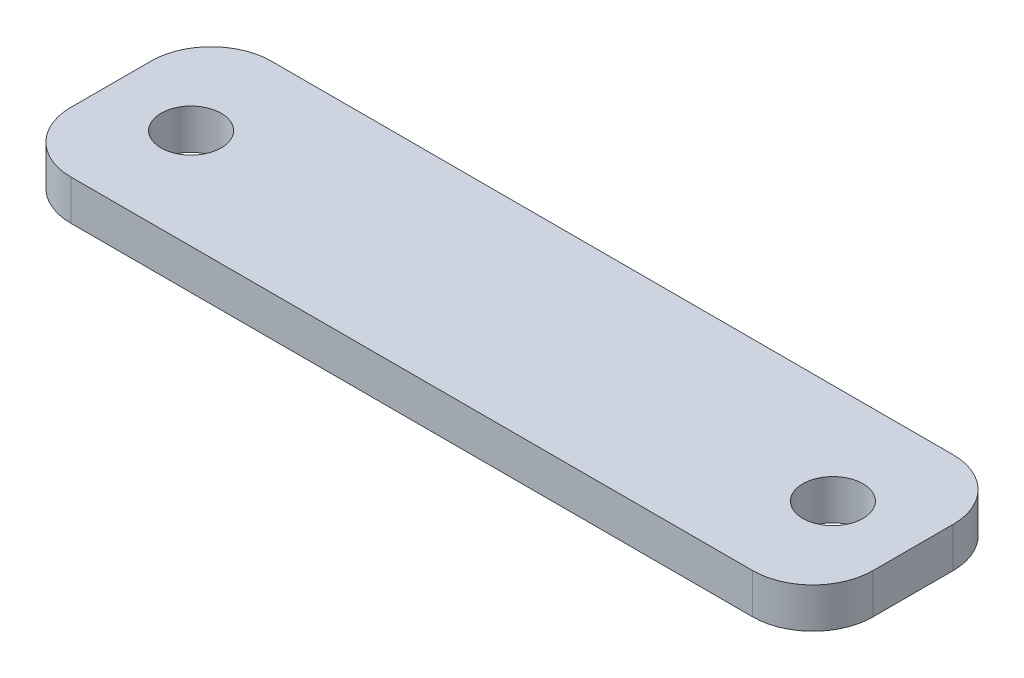
SolidWorks part; units mm, degrees
ref_plane "Front Plane" through (0, 0, 0) normal (0, 0, 1) x (1, 0, 0)
ref_plane "Top Plane" through (0, 0, 0) normal (0, 1, 0) x (1, 0, 0)
ref_plane "Right Plane" through (0, 0, 0) normal (1, 0, 0) x (0, 0, -1)
sketch "Sketch1" plane through (0, 0, 0) normal (0, 1, 0) x (1, 0, 0)
  line L1 (-20, 5) -> (20, 5)
  line L2 (-20, 5) -> (-20, -5)
  line L3 (-20, -5) -> (20, -5)
  line L4 (20, 5) -> (20, -5)
  line L5 (-20, 5) -> (20, -5) construction
  line L6 (-20, -5) -> (20, 5) construction
  point P0 (0, 0)
  dimension "D1" = 10
  dimension "D2" = 40
extrude "Boss-Extrude1" add sketch "Sketch1" along normal blind 2
fillet "Fillet1" radius 3 4 edges at (20, 1, 5) (20, 1, -5) (-20, 1, -5) (-20, 1, 5)
hole_wizard "Ø3.0mm Dowel Hole1" positions "Sketch3" profile "Sketch5" hole size "Ø3.0" standard "ISO" end condition through all
sketch "Sketch3" plane through (0, 2, 0) normal (0, 1, 0) x (1, 0, 0)
  line L0 (20, -2) -> (20, 2) construction
  line L1 (-20, 2) -> (-20, -2) construction
  point P0 (16, 0)
  point P5 (-16, 0)
  point P6 (-39.6904, -0.1283)
  point P7 (9.6041, 0)
  point P8 (0, 0)
  dimension "D1" = 4
  dimension "D2" = 4
sketch "Sketch5" plane through (16, 2, 0) normal (1, 0, 0) x (0, 0, 1)
  line L0 (0, 0) -> (0, 2)
  line L1 (0, 2) -> (1.5, 2)
  line L2 (1.5, 2) -> (1.5, 0)
  line L5 (1.5, 0) -> (0, 0)
  line L11 (0, -22.0399) -> (0, 107.95) construction
  dimension "Thru Hole Dia." = 3
  dimension "Thru Hole Depth" = 2
